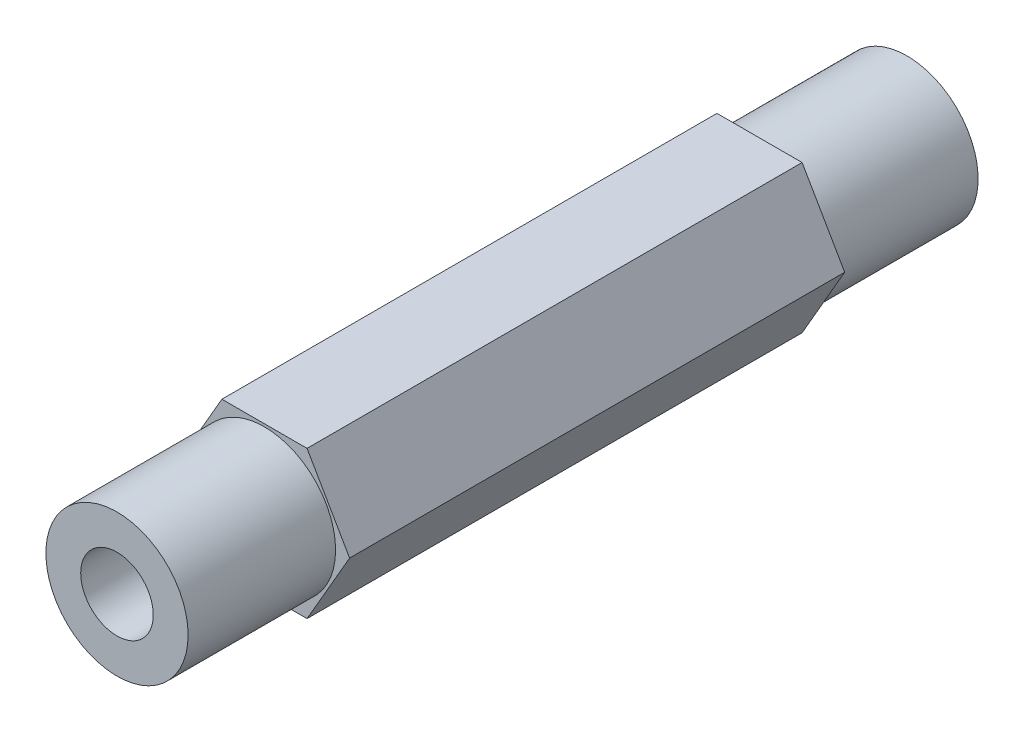
SolidWorks part; units mm, degrees
ref_plane "Front Plane" through (0, 0, 0) normal (1, 0, 0) x (0, 1, 0)
ref_plane "Top Plane" through (0, 0, 0) normal (0, 0, 1) x (0, 1, 0)
ref_plane "Right Plane" through (0, 0, 0) normal (0, 1, 0) x (-1, 0, 0)
sketch "Sketch1" plane through (0, 0, 0) normal (0, 0, 1) x (0, 1, 0)
  line L1 (7.112, -4.1061) -> (7.112, 4.1061)
  line L2 (7.112, 4.1061) -> (0, 8.2122)
  line L3 (0, 8.2122) -> (-7.112, 4.1061)
  line L4 (-7.112, 4.1061) -> (-7.112, -4.1061)
  line L5 (-7.112, -4.1061) -> (0, -8.2122)
  line L6 (0, -8.2122) -> (7.112, -4.1061)
  circle A0 centre (0, 0) radius 7.112 construction
  point P1 (0, 0)
  dimension "D1" = 14.224
extrude "Boss-Extrude1" add sketch "Sketch1" along normal blind 76.2
sketch "Sketch2" plane through (0, 0, 76.2) normal (0, 0, 1) x (1, 0, 0)
  line L6 (8.2122, 0) -> (4.1061, 7.112)
  line L7 (4.1061, 7.112) -> (-4.1061, 7.112)
  line L8 (-4.1061, 7.112) -> (-8.2122, 0)
  line L9 (-8.2122, 0) -> (-4.1061, -7.112)
  line L10 (-4.1061, -7.112) -> (4.1061, -7.112)
  line L11 (4.1061, -7.112) -> (8.2122, 0)
  line L12 (8.2122, 0) -> (4.1061, 7.112)
  line L13 (4.1061, 7.112) -> (-4.1061, 7.112)
  line L14 (-4.1061, 7.112) -> (-8.2122, 0)
  line L15 (-8.2122, 0) -> (-4.1061, -7.112)
  line L16 (-4.1061, -7.112) -> (4.1061, -7.112)
  line L17 (4.1061, -7.112) -> (8.2122, 0)
  circle A0 centre (0, 0) radius 6.86
  dimension "D2" = 13.72
  dimension "D1" = 0
extrude "Cut-Extrude1" cut sketch "Sketch2" against normal blind 14.224
sketch "Sketch3" plane through (0, 0, 0) normal (0, 0, -1) x (1, 0, 0)
  line L6 (4.1061, -7.112) -> (8.2122, 0)
  line L7 (8.2122, 0) -> (4.1061, 7.112)
  line L8 (4.1061, 7.112) -> (-4.1061, 7.112)
  line L9 (-4.1061, 7.112) -> (-8.2122, 0)
  line L10 (-8.2122, 0) -> (-4.1061, -7.112)
  line L11 (-4.1061, -7.112) -> (4.1061, -7.112)
  line L12 (4.1061, -7.112) -> (8.2122, 0)
  line L13 (8.2122, 0) -> (4.1061, 7.112)
  line L14 (4.1061, 7.112) -> (-4.1061, 7.112)
  line L15 (-4.1061, 7.112) -> (-8.2122, 0)
  line L16 (-8.2122, 0) -> (-4.1061, -7.112)
  line L17 (-4.1061, -7.112) -> (4.1061, -7.112)
  circle A0 centre (0, 0) radius 6.86
  dimension "D2" = 13.72
  dimension "D1" = 0
extrude "Cut-Extrude2" cut sketch "Sketch3" against normal blind 14.224
sketch "Sketch4" plane through (0, 0, 0) normal (0, 0, -1) x (1, 0, 0)
  circle A0 centre (0, 0) radius 3.5
  dimension "D1" = 7
extrude "Cut-Extrude3" cut sketch "Sketch4" against normal through all contours A0
